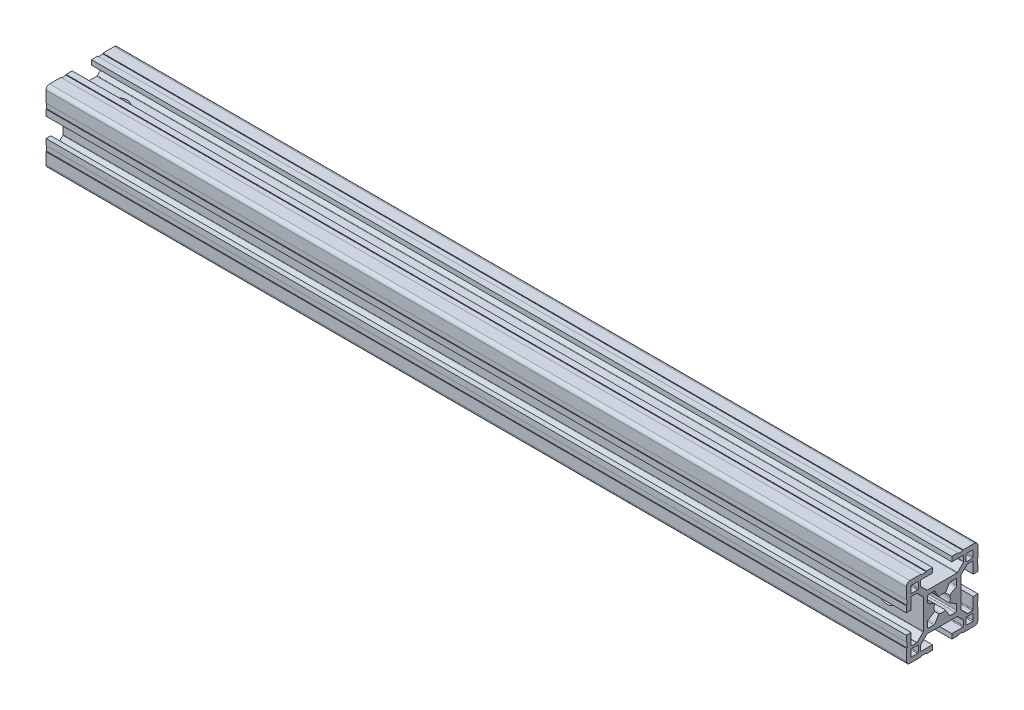
SolidWorks part; units mm, degrees
material "6063-T5"
ref_plane "Plano frontal" through (0, 0, 0) normal (0, 0, 1) x (1, 0, 0)
ref_plane "Plano superior" through (0, 0, 0) normal (0, 1, 0) x (1, 0, 0)
ref_plane "Plano direito" through (0, 0, 0) normal (1, 0, 0) x (0, 0, -1)
sketch "Esboço1" plane through (0, 0, 0) normal (0, 0, 1) x (1, 0, 0)
  line L0 (0, 0) -> (360, 0)
  point P3 (180, 0)
  dimension "D1" = 360
other "Quadrado PF30-11 - PERFIL 3030 CENTRO M8(1)"
ref_plane "Plano1" through (0, 0, 0) normal (1, 0, 0) x (0, 1, 0)
sketch "Sketch1" plane through (0, 0, 0) normal (1, 0, 0) x (0, 1, 0)
  line L0 (-6.1, -3.4254) -> (-6.1, -5.6)
  line L1 (-5.6, -6.1) -> (-3.4254, -6.1)
  line L2 (3.4254, -6.1) -> (5.6, -6.1)
  line L3 (6.1, -5.6) -> (6.1, -3.4254)
  line L4 (6.1, 3.4254) -> (6.1, 5.6)
  line L5 (5.6, 6.1) -> (3.4254, 6.1)
  line L6 (-3.4254, 6.1) -> (-5.6, 6.1)
  line L7 (-6.1, 5.6) -> (-6.1, 3.4254)
  line L8 (15, 6.6) -> (14.7, 6.6)
  line L9 (5.85, -2.9924) -> (3.097, -1.403)
  line L10 (10, 12.7) -> (10, 10.3)
  line L11 (13, -12.7) -> (13, -10.3)
  line L12 (-10.3, -10) -> (-12.7, -10)
  line L13 (-13, 12.7) -> (-13, 10.3)
  line L14 (3.097, 1.403) -> (5.85, 2.9924)
  line L15 (2.9924, 5.85) -> (1.403, 3.097)
  line L16 (-1.403, 3.097) -> (-2.9924, 5.85)
  line L17 (-5.85, 2.9924) -> (-3.097, 1.403)
  line L18 (-3.097, -1.403) -> (-5.85, -2.9924)
  line L19 (-2.9924, -5.85) -> (-1.403, -3.097)
  line L20 (1.403, -3.097) -> (2.9924, -5.85)
  line L21 (10.3, 10) -> (12.7, 10)
  line L22 (13, 10.3) -> (13, 12.7)
  line L23 (12.7, 13) -> (10.3, 13)
  line L24 (12.7, -10) -> (10.3, -10)
  line L25 (10, -10.3) -> (10, -12.7)
  line L26 (10.3, -13) -> (12.7, -13)
  line L27 (-13, -10.3) -> (-13, -12.7)
  line L28 (-12.7, -13) -> (-10.3, -13)
  line L29 (-10, -12.7) -> (-10, -10.3)
  line L30 (-12.7, 10) -> (-10.3, 10)
  line L31 (-10, 10.3) -> (-10, 12.7)
  line L32 (-10.3, 13) -> (-12.7, 13)
  line L33 (15, 4.05) -> (15, 6.6)
  line L34 (13, 4.05) -> (15, 4.05)
  line L35 (13, 8.7) -> (13, 4.05)
  line L36 (10.6799, 9) -> (12.7, 9)
  line L37 (7.9879, 6.4322) -> (10.4678, 8.9121)
  line L38 (7.9, -6.2201) -> (7.9, 6.2201)
  line L39 (10.4678, -8.9121) -> (7.9879, -6.4322)
  line L40 (12.7, -9) -> (10.6799, -9)
  line L41 (13, -4.05) -> (13, -8.7)
  line L42 (15, -4.05) -> (13, -4.05)
  line L43 (15, -6.6) -> (15, -4.05)
  line L44 (14.7, -6.6) -> (15, -6.6)
  line L45 (14.7, -8.8) -> (14.7, -6.6)
  line L46 (15, -8.8) -> (14.7, -8.8)
  line L47 (15, -13.5) -> (15, -8.8)
  line L48 (8.8, -15) -> (13.5, -15)
  line L49 (8.8, -14.7) -> (8.8, -15)
  line L50 (6.6, -14.7) -> (8.8, -14.7)
  line L51 (6.6, -15) -> (6.6, -14.7)
  line L52 (4.05, -15) -> (6.6, -15)
  line L53 (4.05, -13) -> (4.05, -15)
  line L54 (8.7, -13) -> (4.05, -13)
  line L55 (9, -10.6799) -> (9, -12.7)
  line L56 (6.4322, -7.9879) -> (8.9121, -10.4678)
  line L57 (-6.2201, -7.9) -> (6.2201, -7.9)
  line L58 (-8.9121, -10.4678) -> (-6.4322, -7.9879)
  line L59 (-9, -12.7) -> (-9, -10.6799)
  line L60 (-4.05, -13) -> (-8.7, -13)
  line L61 (-4.05, -15) -> (-4.05, -13)
  line L62 (-6.6, -15) -> (-4.05, -15)
  line L63 (-6.6, -14.7) -> (-6.6, -15)
  line L64 (-8.8, -14.7) -> (-6.6, -14.7)
  line L65 (-8.8, -15) -> (-8.8, -14.7)
  line L66 (-13.5, -15) -> (-8.8, -15)
  line L67 (-15, -8.8) -> (-15, -13.5)
  line L68 (-14.7, -8.8) -> (-15, -8.8)
  line L69 (-14.7, -6.6) -> (-14.7, -8.8)
  line L70 (-15, -6.6) -> (-14.7, -6.6)
  line L71 (-15, -4.05) -> (-15, -6.6)
  line L72 (-13, -4.05) -> (-15, -4.05)
  line L73 (-13, -8.7) -> (-13, -4.05)
  line L74 (-10.6799, -9) -> (-12.7, -9)
  line L75 (-7.9879, -6.4322) -> (-10.4678, -8.9121)
  line L76 (-7.9, 6.2201) -> (-7.9, -6.2201)
  line L77 (-10.4678, 8.9121) -> (-7.9879, 6.4322)
  line L78 (-12.7, 9) -> (-10.6799, 9)
  line L79 (-13, 4.05) -> (-13, 8.7)
  line L80 (-15, 4.05) -> (-13, 4.05)
  line L81 (-15, 6.6) -> (-15, 4.05)
  line L82 (-14.7, 6.6) -> (-15, 6.6)
  line L83 (-14.7, 8.8) -> (-14.7, 6.6)
  line L84 (-15, 8.8) -> (-14.7, 8.8)
  line L85 (-15, 13.5) -> (-15, 8.8)
  line L86 (-8.8, 15) -> (-13.5, 15)
  line L87 (-8.8, 14.7) -> (-8.8, 15)
  line L88 (-6.6, 14.7) -> (-8.8, 14.7)
  line L89 (-6.6, 15) -> (-6.6, 14.7)
  line L90 (-4.05, 15) -> (-6.6, 15)
  line L91 (-4.05, 13) -> (-4.05, 15)
  line L92 (-8.7, 13) -> (-4.05, 13)
  line L93 (-9, 10.6799) -> (-9, 12.7)
  line L94 (-6.4322, 7.9879) -> (-8.9121, 10.4678)
  line L95 (6.2201, 7.9) -> (-6.2201, 7.9)
  line L96 (8.9121, 10.4678) -> (6.4322, 7.9879)
  line L97 (9, 12.7) -> (9, 10.6799)
  line L98 (4.05, 13) -> (8.7, 13)
  line L99 (4.05, 15) -> (4.05, 13)
  line L100 (6.6, 15) -> (4.05, 15)
  line L101 (6.6, 14.7) -> (6.6, 15)
  line L102 (8.8, 14.7) -> (6.6, 14.7)
  line L103 (8.8, 15) -> (8.8, 14.7)
  line L104 (13.5, 15) -> (8.8, 15)
  line L105 (15, 8.8) -> (15, 13.5)
  line L106 (14.7, 8.8) -> (15, 8.8)
  line L107 (14.7, 6.6) -> (14.7, 8.8)
  arc A0 (-5.85, -2.9924) -> (-6.1, -3.4254) centre (-5.6, -3.4254) ccw
  arc A1 (-6.1, -5.6) -> (-5.6, -6.1) centre (-5.6, -5.6) ccw
  arc A2 (-3.4254, -6.1) -> (-2.9924, -5.85) centre (-3.4254, -5.6) ccw
  arc A3 (2.9924, -5.85) -> (3.4254, -6.1) centre (3.4254, -5.6) ccw
  arc A4 (5.6, -6.1) -> (6.1, -5.6) centre (5.6, -5.6) ccw
  arc A5 (6.1, -3.4254) -> (5.85, -2.9924) centre (5.6, -3.4254) ccw
  arc A6 (5.85, 2.9924) -> (6.1, 3.4254) centre (5.6, 3.4254) ccw
  arc A7 (6.1, 5.6) -> (5.6, 6.1) centre (5.6, 5.6) ccw
  arc A8 (3.4254, 6.1) -> (2.9924, 5.85) centre (3.4254, 5.6) ccw
  arc A9 (-2.9924, 5.85) -> (-3.4254, 6.1) centre (-3.4254, 5.6) ccw
  arc A10 (-5.6, 6.1) -> (-6.1, 5.6) centre (-5.6, 5.6) ccw
  arc A11 (-6.1, 3.4254) -> (-5.85, 2.9924) centre (-5.6, 3.4254) ccw
  arc A12 (3.097, -1.403) -> (3.097, 1.403) centre (0, 0) ccw
  arc A13 (1.403, 3.097) -> (-1.403, 3.097) centre (0, 0) ccw
  arc A14 (-3.097, 1.403) -> (-3.097, -1.403) centre (0, 0) ccw
  arc A15 (-1.403, -3.097) -> (1.403, -3.097) centre (0, 0) ccw
  arc A16 (10, 10.3) -> (10.3, 10) centre (10.3, 10.3) ccw
  arc A17 (12.7, 10) -> (13, 10.3) centre (12.7, 10.3) ccw
  arc A18 (13, 12.7) -> (12.7, 13) centre (12.7, 12.7) ccw
  arc A19 (10.3, 13) -> (10, 12.7) centre (10.3, 12.7) ccw
  arc A20 (13, -10.3) -> (12.7, -10) centre (12.7, -10.3) ccw
  arc A21 (10.3, -10) -> (10, -10.3) centre (10.3, -10.3) ccw
  arc A22 (10, -12.7) -> (10.3, -13) centre (10.3, -12.7) ccw
  arc A23 (12.7, -13) -> (13, -12.7) centre (12.7, -12.7) ccw
  arc A24 (-12.7, -10) -> (-13, -10.3) centre (-12.7, -10.3) ccw
  arc A25 (-13, -12.7) -> (-12.7, -13) centre (-12.7, -12.7) ccw
  arc A26 (-10.3, -13) -> (-10, -12.7) centre (-10.3, -12.7) ccw
  arc A27 (-10, -10.3) -> (-10.3, -10) centre (-10.3, -10.3) ccw
  arc A28 (-13, 10.3) -> (-12.7, 10) centre (-12.7, 10.3) ccw
  arc A29 (-10.3, 10) -> (-10, 10.3) centre (-10.3, 10.3) ccw
  arc A30 (-10, 12.7) -> (-10.3, 13) centre (-10.3, 12.7) ccw
  arc A31 (-12.7, 13) -> (-13, 12.7) centre (-12.7, 12.7) ccw
  arc A32 (13, 8.7) -> (12.7, 9) centre (12.7, 8.7) ccw
  arc A33 (10.6799, 9) -> (10.4678, 8.9121) centre (10.6799, 8.7) ccw
  arc A34 (7.9879, 6.4322) -> (7.9, 6.2201) centre (8.2, 6.2201) ccw
  arc A35 (7.9, -6.2201) -> (7.9879, -6.4322) centre (8.2, -6.2201) ccw
  arc A36 (10.4678, -8.9121) -> (10.6799, -9) centre (10.6799, -8.7) ccw
  arc A37 (12.7, -9) -> (13, -8.7) centre (12.7, -8.7) ccw
  arc A38 (13.5, -15) -> (15, -13.5) centre (13.5, -13.5) ccw
  arc A39 (8.7, -13) -> (9, -12.7) centre (8.7, -12.7) ccw
  arc A40 (9, -10.6799) -> (8.9121, -10.4678) centre (8.7, -10.6799) ccw
  arc A41 (6.4322, -7.9879) -> (6.2201, -7.9) centre (6.2201, -8.2) ccw
  arc A42 (-6.2201, -7.9) -> (-6.4322, -7.9879) centre (-6.2201, -8.2) ccw
  arc A43 (-8.9121, -10.4678) -> (-9, -10.6799) centre (-8.7, -10.6799) ccw
  arc A44 (-9, -12.7) -> (-8.7, -13) centre (-8.7, -12.7) ccw
  arc A45 (-15, -13.5) -> (-13.5, -15) centre (-13.5, -13.5) ccw
  arc A46 (-13, -8.7) -> (-12.7, -9) centre (-12.7, -8.7) ccw
  arc A47 (-10.6799, -9) -> (-10.4678, -8.9121) centre (-10.6799, -8.7) ccw
  arc A48 (-7.9879, -6.4322) -> (-7.9, -6.2201) centre (-8.2, -6.2201) ccw
  arc A49 (-7.9, 6.2201) -> (-7.9879, 6.4322) centre (-8.2, 6.2201) ccw
  arc A50 (-10.4678, 8.9121) -> (-10.6799, 9) centre (-10.6799, 8.7) ccw
  arc A51 (-12.7, 9) -> (-13, 8.7) centre (-12.7, 8.7) ccw
  arc A52 (-13.5, 15) -> (-15, 13.5) centre (-13.5, 13.5) ccw
  arc A53 (-8.7, 13) -> (-9, 12.7) centre (-8.7, 12.7) ccw
  arc A54 (-9, 10.6799) -> (-8.9121, 10.4678) centre (-8.7, 10.6799) ccw
  arc A55 (-6.4322, 7.9879) -> (-6.2201, 7.9) centre (-6.2201, 8.2) ccw
  arc A56 (6.2201, 7.9) -> (6.4322, 7.9879) centre (6.2201, 8.2) ccw
  arc A57 (8.9121, 10.4678) -> (9, 10.6799) centre (8.7, 10.6799) ccw
  arc A58 (9, 12.7) -> (8.7, 13) centre (8.7, 12.7) ccw
  arc A59 (15, 13.5) -> (13.5, 15) centre (13.5, 13.5) ccw
  point P1 (0, 0)
  point P2 (0, 0)
  point P3 (-15, -15)
  point P4 (0, -15)
  point P5 (-15, 0)
  point P230 (-15, 15)
  point P231 (0, 15)
  point P232 (15, 15)
  point P233 (15, 0)
  point P234 (15, -15)
  point P235 (0, -15)
  point P236 (-15, -15)
  point P237 (-15, 0)
  point P238 (0, 0)
  point P239 (0, 0)
sketch "Esboço2" plane through (0, 0, -7.9) normal (0, 0, -1) x (-1, 0, 0)
  line L0 (-360, -6.2201) -> (-360, 6.2201) construction
  circle A1 centre (-345, 0) radius 3.95
  point P5 (-360, 0)
  dimension "D1" = 15
  dimension "D2" = 7.9
extrude "Corte-extrusão1" cut sketch "Esboço2" against normal through all
sketch "Esboço3" plane through (0, 7.9, 0) normal (0, 1, 0) x (1, 0, 0)
  line L0 (0, 6.2201) -> (0, -6.2201) construction
  circle A0 centre (15, 0) radius 3.95
  point P4 (15, 2.8437)
  dimension "D2" = 7.9
  dimension "D1" = 15
extrude "Corte-extrusão2" cut sketch "Esboço3" against normal through all
